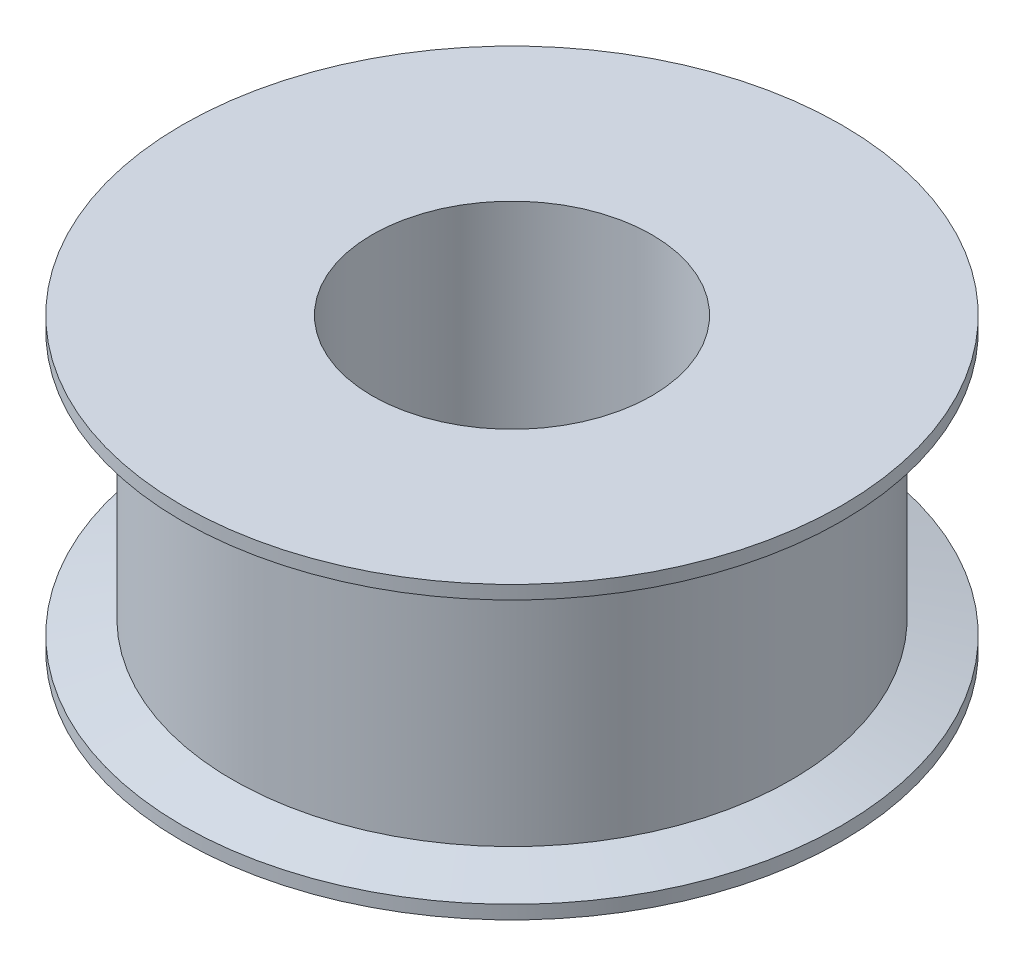
SolidWorks part; units mm, degrees
ref_plane "Front Plane" through (0, 0, 0) normal (0, 0, 1) x (1, 0, 0)
ref_plane "Top Plane" through (0, 0, 0) normal (0, 1, 0) x (1, 0, 0)
ref_plane "Right Plane" through (0, 0, 0) normal (1, 0, 0) x (0, 0, -1)
sketch "Sketch1" plane through (0, 0, 0) normal (0, 0, 1) x (1, 0, 0)
  line L0 (0, 0) -> (0, 101.3948) construction
  line L1 (-5.872, 6.604) -> (39.5917, 6.604) construction
  line L2 (6.3513, 0) -> (6.3513, 13.208)
  line L3 (6.3513, 13.208) -> (14.986, 13.208)
  line L4 (14.986, 13.208) -> (14.986, 12.5935)
  line L5 (14.986, 12.5935) -> (12.7, 11.938)
  line L6 (12.7, 11.938) -> (12.7, 1.27)
  line L7 (14.986, 0.6145) -> (12.7, 1.27)
  line L8 (14.986, 0) -> (14.986, 0.6145)
  line L9 (6.3513, 0) -> (14.986, 0)
  line L10 (14.986, 12.5935) -> (9.2966, 12.5935) construction
  point P12 (12.7, 6.604)
  point P15 (6.3513, 6.604)
  dimension "D1" = 12.7025
  dimension "D2" = 29.972
  dimension "D3" = 25.4
  dimension "D4" = 6.604
  dimension "D5" = 16
  dimension "D6" = 6.604
  dimension "D7" = 5.334
revolve "Revolve1" add sketch "Sketch1" angle 360 about L0
